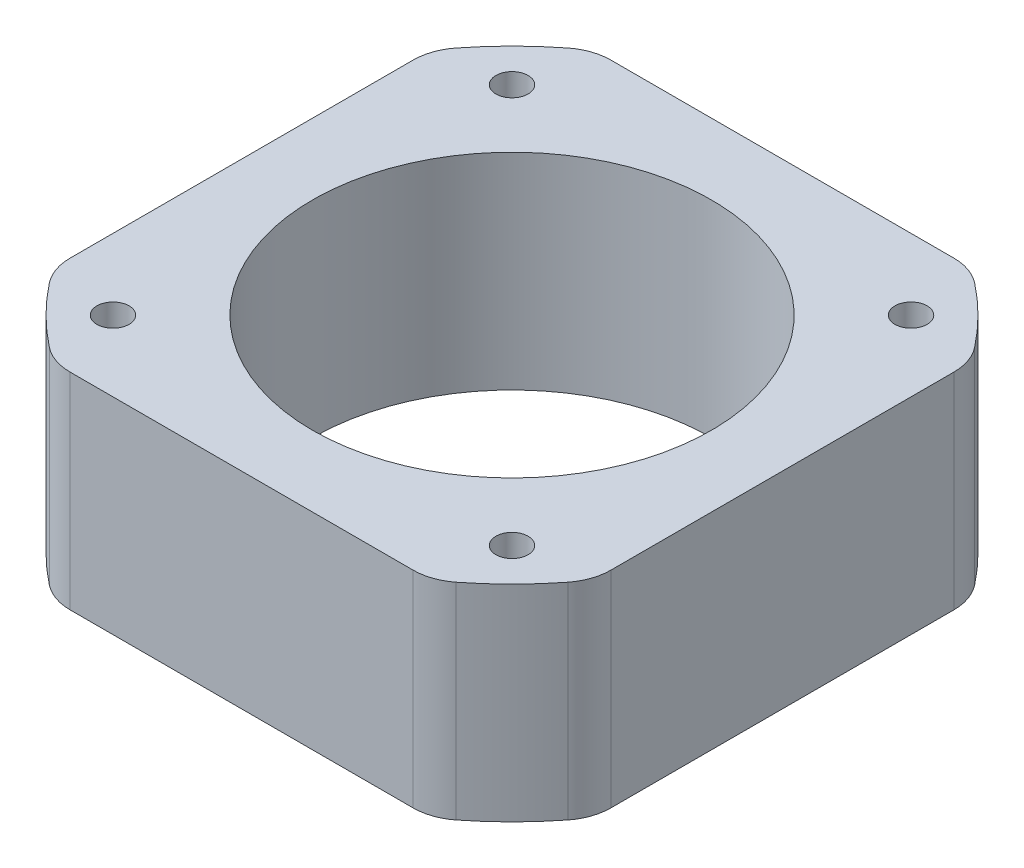
SolidWorks part; units mm, degrees
ref_plane "Спереди" through (0, 0, 0) normal (0, 0, 1) x (1, 0, 0)
ref_plane "Сверху" through (0, 0, 0) normal (0, 1, 0) x (1, 0, 0)
ref_plane "Справа" through (0, 0, 0) normal (1, 0, 0) x (0, 0, -1)
sketch "Эскиз1" plane through (0, 0, 0) normal (0, 1, 0) x (1, 0, 0)
  line L1 (-14.641, -21) -> (14.641, -21)
  line L2 (-21, -14.641) -> (-21, 14.641)
  line L3 (-14.641, 21) -> (14.641, 21)
  line L4 (21, -14.641) -> (21, 14.641)
  line L5 (-21, -21) -> (21, 21) construction
  line L6 (-21, 21) -> (21, -21) construction
  line L10 (-15.5, -15.5) -> (15.5, -15.5) construction
  line L11 (-15.5, -15.5) -> (-15.5, 15.5) construction
  line L12 (-15.5, 15.5) -> (15.5, 15.5) construction
  line L13 (15.5, -15.5) -> (15.5, 15.5) construction
  line L14 (-15.5, -15.5) -> (15.5, 15.5) construction
  line L15 (-15.5, 15.5) -> (15.5, -15.5) construction
  circle A0 centre (-15.5, 15.5) radius 1.25
  circle A1 centre (15.5, 15.5) radius 1.25
  circle A2 centre (15.5, -15.5) radius 1.25
  circle A3 centre (-15.5, -15.5) radius 1.25
  circle A4 centre (0, 0) radius 15.5
  arc A7 (-21, -14.641) -> (-14.641, -21) centre (0, 0) ccw
  arc A8 (-14.641, 21) -> (-21, 14.641) centre (0, 0) ccw
  arc A9 (21, 14.641) -> (14.641, 21) centre (0, 0) ccw
  arc A10 (14.641, -21) -> (21, -14.641) centre (0, 0) ccw
  point P0 (0, 0)
  point P13 (0, 0)
  dimension "D9" = 2.5
  dimension "D14" = 25.6
  dimension "D15" = 31
  dimension "D16" = 42
extrude "Бобышка-Вытянуть1" add sketch "Эскиз1" along normal blind 16
fillet "Скругление1" radius 4 8 edges at (-21, 8, -14.641) (-14.641, 8, -21) (14.641, 8, -21) (21, 8, -14.641) (21, 8, 14.641) (14.641, 8, 21) (-14.641, 8, 21) (-21, 8, 14.641)
